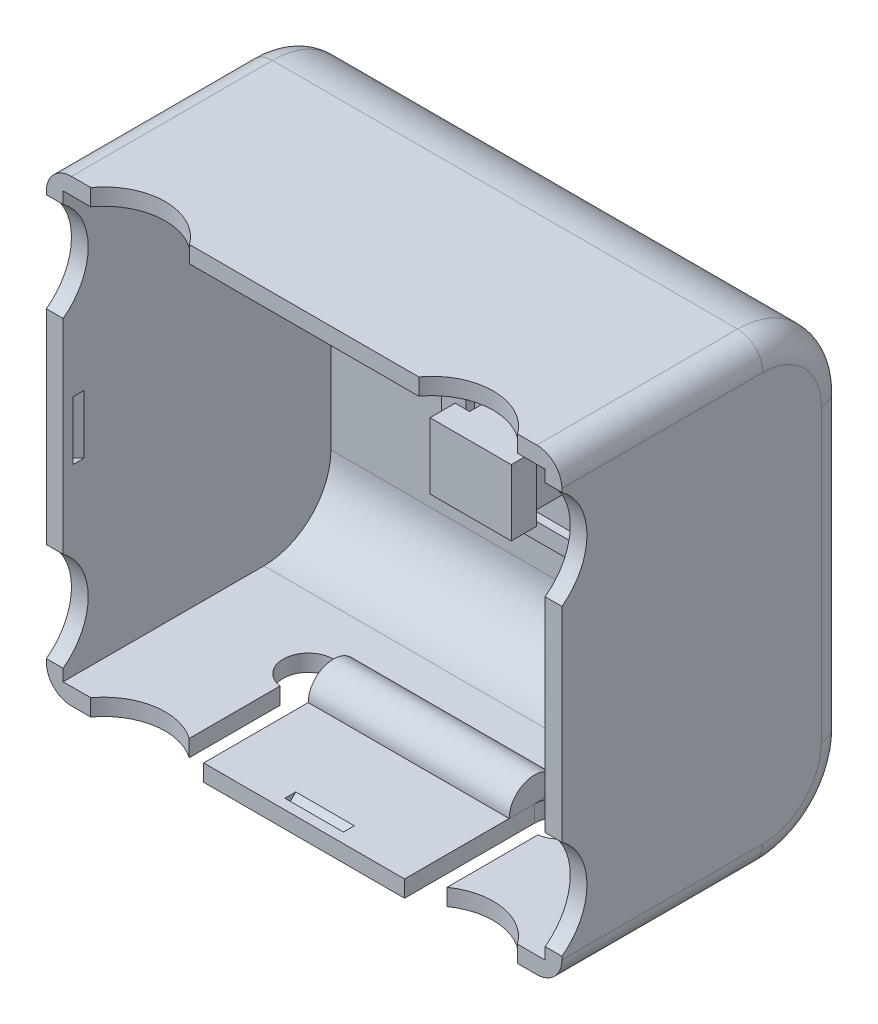
SolidWorks part; units mm, degrees
ref_plane "正面" through (0, 0, 0) normal (0, 0, 1) x (1, 0, 0)
ref_plane "平面" through (0, 0, 0) normal (0, 1, 0) x (1, 0, 0)
ref_plane "右側面" through (0, 0, 0) normal (1, 0, 0) x (0, 0, -1)
sketch "ｽｹｯﾁ1" plane through (0, 0, 0) normal (0, 0, 1) x (1, 0, 0)
  line L0 (0, 0) -> (54, 0) construction
  line L1 (0, 20) -> (54, 20) construction
  line L2 (-1.5, 45.5) -> (55.5, 45.5)
  line L3 (54, 0) -> (54, 40) construction
  line L4 (54, 40) -> (0, 40) construction
  line L5 (0, 40) -> (0, 0) construction
  line L6 (55.5, 45.5) -> (55.5, -5.5)
  line L7 (55.5, -5.5) -> (-1.5, -5.5)
  line L8 (-1.5, -5.5) -> (-1.5, 45.5)
  line L9 (27, 45.5) -> (27, -5.5) construction
  circle A0 centre (2, 2) radius 1.1 construction
  circle A1 centre (52, 2) radius 1.1 construction
  circle A2 centre (52, 38) radius 1.1 construction
  circle A3 centre (2, 38) radius 1.1 construction
  circle A4 centre (2, 38) radius 0.9
  circle A5 centre (2, 38) radius 1.8491
  circle A6 centre (2, 2) radius 1.8491
  circle A7 centre (52, 2) radius 1.8491
  circle A8 centre (52, 38) radius 1.8491
  circle A9 centre (52, 38) radius 0.9
  circle A10 centre (52, 2) radius 0.9
  circle A11 centre (2, 2) radius 0.9
  circle A12 centre (11.0176, 28.1) radius 7
  circle A13 centre (42.9824, 28.1) radius 7
  circle A14 centre (16.5, 8.4) radius 7
  circle A15 centre (37.5, 8.4) radius 7
  dimension "D3" = 2.2
  dimension "D8" = 1.8
  dimension "D9" = 14
  dimension "D10" = 14
  dimension "D11" = 14
  dimension "D12" = 14
  dimension "D1" = 40
  dimension "D2" = 54
  dimension "D4" = 25.5
  dimension "D5" = 25.5
  dimension "D6" = 1.5
  dimension "D7" = 1.5
sketch "ｽｹｯﾁ2" plane through (0, 0, 0) normal (1, 0, 0) x (0, 0, -1)
  line L2 (0, 0) -> (24, 0)
  line L3 (0, 0) -> (0, 54.8)
  line L4 (0, 54.8) -> (24, 54.8)
  line L5 (34, 10) -> (34, 44.8)
  arc A0 (24, 0) -> (34, 10) centre (24, 10) ccw
  arc A1 (24, 54.8) -> (34, 44.8) centre (24, 44.8) cw
  point P8 (34, 54.8)
  dimension "D3" = 10
  dimension "D1" = 34
  dimension "D2" = 54.8
extrude "ﾎﾞｽ - 押し出し1" add sketch "ｽｹｯﾁ2" along normal blind 61.6
shell "ｼｪﾙ1" thickness 2
fillet "ﾌｨﾚｯﾄ2" radius 3 10 edges at (0, 54.8, -12) (61.6, 54.8, -12) (0, 0, -12) (0, 2.9289, -31.0711) (0, 27.4, -34) (0, 51.8711, -31.0711) (61.6, 0, -12) (61.6, 2.9289, -31.0711) (61.6, 27.4, -34) (61.6, 51.8711, -31.0711)
sketch "ｽｹｯﾁ3" plane through (0, 0, -34) normal (0, 0, -1) x (-1, 0, 0)
  line L0 (-30.8, 44.8) -> (-30.8, 10) construction
  line L1 (-58.6, 44.8) -> (-3, 44.8) construction
  line L2 (-58.6, 10) -> (-3, 10) construction
  line L3 (-30.8, 39.225) -> (-30.8, 15.575) construction
  line L4 (-24.3025, 31.1) -> (-24.3025, 39.225) construction
  line L5 (-34.9975, 31.1) -> (-34.9975, 23.7)
  line L6 (-26.6025, 31.1) -> (-26.6025, 23.7)
  line L7 (-39.5975, 31.1) -> (-34.9975, 31.1)
  line L8 (-39.5975, 31.1) -> (-39.5975, 23.7)
  line L9 (-39.5975, 23.7) -> (-34.9975, 23.7)
  line L10 (-37.2975, 39.225) -> (-37.2975, 15.575) construction
  line L11 (-22.0025, 23.7) -> (-26.6025, 23.7)
  line L12 (-22.0025, 31.1) -> (-22.0025, 23.7)
  line L13 (-22.0025, 31.1) -> (-26.6025, 31.1)
  line L14 (-30.8, 27.4) -> (-58.6, 27.4) construction
  line L15 (-58.6, 44.8) -> (-58.6, 10) construction
extrude "ｶｯﾄ - 押し出し1" cut sketch "ｽｹｯﾁ3" against normal up to next
sketch "ｽｹｯﾁ4" plane through (0, 0, -34) normal (0, 0, 1) x (1, 0, 0)
  line L6 (22.0025, 31.1) -> (26.6025, 31.1) construction
  line L7 (22.0025, 23.7) -> (22.0025, 31.1) construction
  line L8 (22.0025, 23.7) -> (26.6025, 23.7) construction
  line L9 (26.6025, 31.1) -> (26.6025, 23.7) construction
  line L10 (39.5975, 23.7) -> (34.9975, 23.7) construction
  line L11 (34.9975, 31.1) -> (34.9975, 23.7) construction
  line L12 (17.9225, 15.575) -> (30.6725, 15.575)
  line L13 (30.6725, 15.575) -> (43.6775, 15.575)
  line L14 (43.6775, 15.575) -> (43.6775, 39.225)
  line L15 (43.6775, 39.225) -> (30.6725, 39.225)
  line L16 (30.6725, 39.225) -> (17.9225, 39.225)
  line L17 (17.9225, 39.225) -> (17.9225, 15.575)
  line L18 (39.5975, 31.1) -> (34.9975, 31.1) construction
  line L19 (39.5975, 31.1) -> (39.5975, 23.7) construction
  line L20 (22.0025, 31.1) -> (26.6025, 31.1)
  line L21 (22.0025, 23.7) -> (22.0025, 31.1)
  line L22 (22.0025, 23.7) -> (26.6025, 23.7)
  line L23 (26.6025, 31.1) -> (26.6025, 23.7)
  line L24 (39.5975, 23.7) -> (34.9975, 23.7)
  line L25 (34.9975, 31.1) -> (34.9975, 23.7)
  line L26 (39.5975, 31.1) -> (34.9975, 31.1)
  line L27 (39.5975, 31.1) -> (39.5975, 23.7)
extrude "ﾎﾞｽ - 押し出し2" add sketch "ｽｹｯﾁ4" along normal blind 3.7
sketch "ｽｹｯﾁ5" plane through (0, 0, -30.3) normal (0, 0, 1) x (1, 0, 0)
  line L9 (20.8725, 31.35) -> (20.8725, 23.45)
  line L10 (17.9225, 31.35) -> (17.9225, 23.45)
  line L11 (43.6775, 31.35) -> (43.6775, 23.45)
  line L12 (40.7275, 23.45) -> (40.7275, 31.35)
  line L13 (43.6775, 37.225) -> (43.6775, 39.225)
  line L14 (43.6775, 39.225) -> (17.9225, 39.225)
  line L15 (17.9225, 37.225) -> (43.6775, 37.225)
  line L16 (43.6775, 17.575) -> (17.9225, 17.575)
  line L17 (17.9225, 15.575) -> (43.6775, 15.575)
  line L18 (17.9225, 31.35) -> (20.8725, 31.35)
  line L19 (17.9225, 23.45) -> (20.8725, 23.45)
  line L20 (40.7275, 31.35) -> (43.6775, 31.35)
  line L21 (40.7275, 23.45) -> (43.6775, 23.45)
  line L22 (17.9225, 39.225) -> (17.9225, 37.225)
  line L23 (17.9225, 17.575) -> (17.9225, 15.575)
  line L24 (43.6775, 17.575) -> (43.6775, 15.575)
extrude "ﾎﾞｽ - 押し出し3" add sketch "ｽｹｯﾁ5" along normal blind 1
ref_plane "平面1" through (-6.5183, 23.4524, -44.2238) normal (0, 1, 0) x (1, 0, 0)
sketch "ｽｹｯﾁ6" plane through (-6.5183, 23.4524, -44.2238) normal (0, 1, 0) x (1, 0, 0)
  line L0 (34.1908, -13.9238) -> (40.4458, -13.9238)
  line L1 (40.4458, -13.9238) -> (40.4458, -21.3238)
  line L2 (40.4458, -21.3238) -> (42.1708, -21.3238)
  line L3 (42.1708, -21.3238) -> (42.1708, -24.3238)
  line L4 (42.1708, -24.3238) -> (32.4658, -24.3238)
  line L5 (32.4658, -24.3238) -> (32.4658, -21.3238)
  line L6 (32.4658, -21.3238) -> (34.1908, -21.3238)
  line L7 (34.1908, -21.3238) -> (34.1908, -13.9238)
extrude "ﾎﾞｽ - 押し出し4" add sketch "ｽｹｯﾁ6" along normal up to vertex (7.8976 mm away)
sketch "ｽｹｯﾁ8" plane through (0, 0, 0) normal (-1, 0, 0) x (0, 0, 1)
  line L0 (0, 51.8) -> (0, 3) construction
  line L1 (0, 51.3992) -> (0, 39.6008)
  line L2 (0, 15.1992) -> (0, 3.4008)
  arc A0 (0, 51.3992) -> (0, 39.6008) centre (4.3, 45.5) ccw
  arc A1 (0, 15.1992) -> (0, 3.4008) centre (4.3, 9.3) ccw
extrude "ｶｯﾄ - 押し出し3" cut sketch "ｽｹｯﾁ8" against normal up to vertex
sketch "ｽｹｯﾁ9" plane through (0, 0, 0) normal (0, -1, 0) x (1, 0, 0)
  line L0 (58.6, 0) -> (3, 0) construction
  line L1 (56.2992, 0) -> (44.5008, 0)
  line L2 (17.0992, 0) -> (5.3008, 0)
  arc A0 (44.5008, 0) -> (56.2992, 0) centre (50.4, 4.3) ccw
  arc A1 (5.3008, 0) -> (17.0992, 0) centre (11.2, 4.3) ccw
extrude "ｶｯﾄ - 押し出し4" cut sketch "ｽｹｯﾁ9" against normal up to vertex
ref_plane "平面2" through (0, 27.4, 0) normal (0, -1, 0) x (-1, 0, 0)
sketch "ｽｹｯﾁ11" plane through (0, 27.4, 0) normal (0, -1, 0) x (-1, 0, 0)
  line L0 (-59.6, 0) -> (-59.6, 24) construction
  line L1 (-59.6, 1.1766) -> (-59.6, 2.4767)
  line L2 (-59.6, 2.3353) -> (-60.1887, 1.7466) construction
  line L3 (-60.1887, 1.7466) -> (-60.1887, 1.2766) construction
  line L4 (-60.1887, 1.2766) -> (-59.6, 1.2766) construction
  line L5 (-60.2887, 1.788) -> (-59.6, 2.4767)
  line L6 (-60.2887, 1.788) -> (-60.2887, 1.1766)
  line L7 (-60.2887, 1.1766) -> (-59.6, 1.1766)
  line L8 (-59.6707, 2.406) -> (-60.2887, 1.788) construction
  line L9 (-30.8, 34) -> (-30.8, 48.4859) construction
  line L10 (-58.6, 34) -> (-3, 34) construction
  line L11 (-1.4113, 1.7466) -> (-1.4113, 1.2766) construction
  line L12 (-2, 2.3353) -> (-1.4113, 1.7466) construction
  line L13 (-1.3113, 1.1766) -> (-2, 1.1766)
  line L14 (-1.3113, 1.788) -> (-1.3113, 1.1766)
  line L15 (-1.3113, 1.788) -> (-2, 2.4767)
  line L16 (-1.4113, 1.2766) -> (-2, 1.2766) construction
  line L17 (-2, 1.1766) -> (-2, 2.4767)
  dimension "D1" = 0.1
  dimension "D2" = 0
extrude "ｶｯﾄ - 押し出し5" cut sketch "ｽｹｯﾁ11" against normal mid plane 7
ref_plane "平面3" through (30.8, 0, 0) normal (1, 0, 0) x (0, 0, -1)
sketch "ｽｹｯﾁ12" plane through (30.8, 0, 0) normal (1, 0, 0) x (0, 0, -1)
  line L0 (1.7713, 1.4113) -> (1.3013, 1.4113) construction
  line L1 (2.36, 2) -> (1.7713, 1.4113) construction
  line L2 (2.5014, 2) -> (1.2013, 2)
  line L3 (2.36, 52.8) -> (1.7713, 53.3887) construction
  line L4 (1.7713, 53.3887) -> (1.3013, 53.3887) construction
  line L5 (1.3013, 53.3887) -> (1.3013, 52.8) construction
  line L6 (1.8128, 53.4887) -> (2.5014, 52.8)
  line L7 (1.8128, 53.4887) -> (1.2013, 53.4887)
  line L8 (1.2013, 53.4887) -> (1.2013, 52.8)
  line L9 (2.4307, 52.8707) -> (1.8128, 53.4887) construction
  line L10 (24, 52.8) -> (0, 52.8) construction
  line L11 (2.5014, 52.8) -> (1.2013, 52.8)
  line L12 (34, 27.4) -> (38.8234, 27.4) construction
  line L13 (34, 44.8) -> (34, 10) construction
  line L14 (1.2013, 1.3113) -> (1.2013, 2)
  line L15 (1.8128, 1.3113) -> (1.2013, 1.3113)
  line L16 (1.8128, 1.3113) -> (2.5014, 2)
  dimension "D2" = 0
  dimension "D1" = 0.1
extrude "ｶｯﾄ - 押し出し6" cut sketch "ｽｹｯﾁ12" against normal mid plane 7
sketch "ｽｹｯﾁ13" plane through (0, 0, 0) normal (0, -1, 0) x (1, 0, 0)
  line L1 (15.396, 0) -> (15.396, -12.5268)
  line L2 (42.804, -15.5) -> (45.804, -15.5) construction
  line L3 (42.804, -12.5) -> (45.804, -12.5) construction
  line L4 (46.204, 0) -> (42.804, 0)
  line L5 (30.8, -34) -> (30.8, -54.1589) construction
  line L6 (58.6, -34) -> (3, -34) construction
  line L7 (30.8, -17.05) -> (30.8, 17.05) construction
  line L8 (18.796, 0) -> (18.796, -15.5)
  line L9 (15.396, 0) -> (18.796, 0)
  line L10 (42.804, 0) -> (42.804, -15.5)
  line L11 (18.796, -12.5) -> (15.796, -12.5) construction
  line L12 (46.204, 0) -> (46.204, -12.5268)
  line L13 (18.796, -15.5) -> (15.796, -15.5) construction
  line L14 (15.796, -12.5) -> (15.796, -15.5) construction
  arc A0 (15.396, -12.5268) -> (18.796, -15.5) centre (15.796, -15.5) ccw
  arc A1 (46.204, -12.5268) -> (42.804, -15.5) centre (45.804, -15.5) cw
  dimension "D3" = 3
  dimension "D4" = 3
extrude "ｶｯﾄ - 押し出し7" cut sketch "ｽｹｯﾁ13" against normal up to vertex
sketch "ｽｹｯﾁ14" plane through (18.796, 0, 0) normal (-1, 0, 0) x (0, 0, 1)
  line L0 (0, 2) -> (-24, 2) construction
  line L1 (-12.5, 2) -> (-18.5, 2)
  arc A0 (-12.5, 2) -> (-18.5, 2) centre (-15.5, 2) ccw
extrude "ﾎﾞｽ - 押し出し5" add sketch "ｽｹｯﾁ14" against normal blind 24.01
